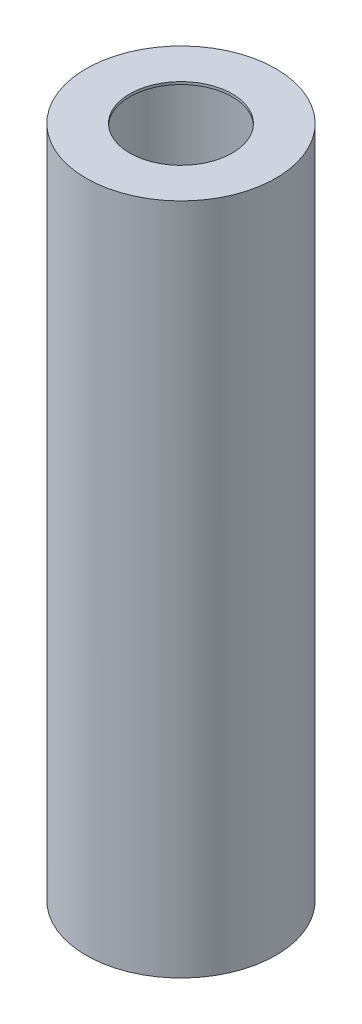
SolidWorks part; units mm, degrees
material "PVC 0.007 Plasticized"
ref_plane "Front" through (0, 0, 0) normal (0, 0, 1) x (1, 0, 0)
ref_plane "Top" through (0, 0, 0) normal (0, 1, 0) x (1, 0, 0)
ref_plane "Right" through (0, 0, 0) normal (1, 0, 0) x (0, 0, -1)
sketch "Sketch1" plane through (0, 0, 0) normal (0, 1, 0) x (1, 0, 0)
  circle A0 centre (0, 0) radius 9.25
  circle A1 centre (0, 0) radius 9
  dimension "D1" = 18.5
  dimension "D2" = 18
extrude "Boss-Extrude1" add sketch "Sketch1" along normal blind 65.1
sketch "Sketch2" plane through (0, 65.1, 0) normal (0, 1, 0) x (1, 0, 0)
  circle A0 centre (0, 0) radius 9.25 construction
  circle A1 centre (0, 0) radius 9.25
  circle A2 centre (0, 0) radius 5
  dimension "D1" = 10
extrude "Boss-Extrude2" add sketch "Sketch2" along normal blind 0.25
sketch "Sketch3" plane through (0, 0, 0) normal (0, -1, 0) x (1, 0, 0)
  circle A0 centre (0, 0) radius 9.25 construction
  circle A1 centre (0, 0) radius 9.25
  circle A2 centre (-0.1724, 0) radius 5
  dimension "D1" = 10
extrude "Boss-Extrude3" add sketch "Sketch3" along normal blind 0.25
